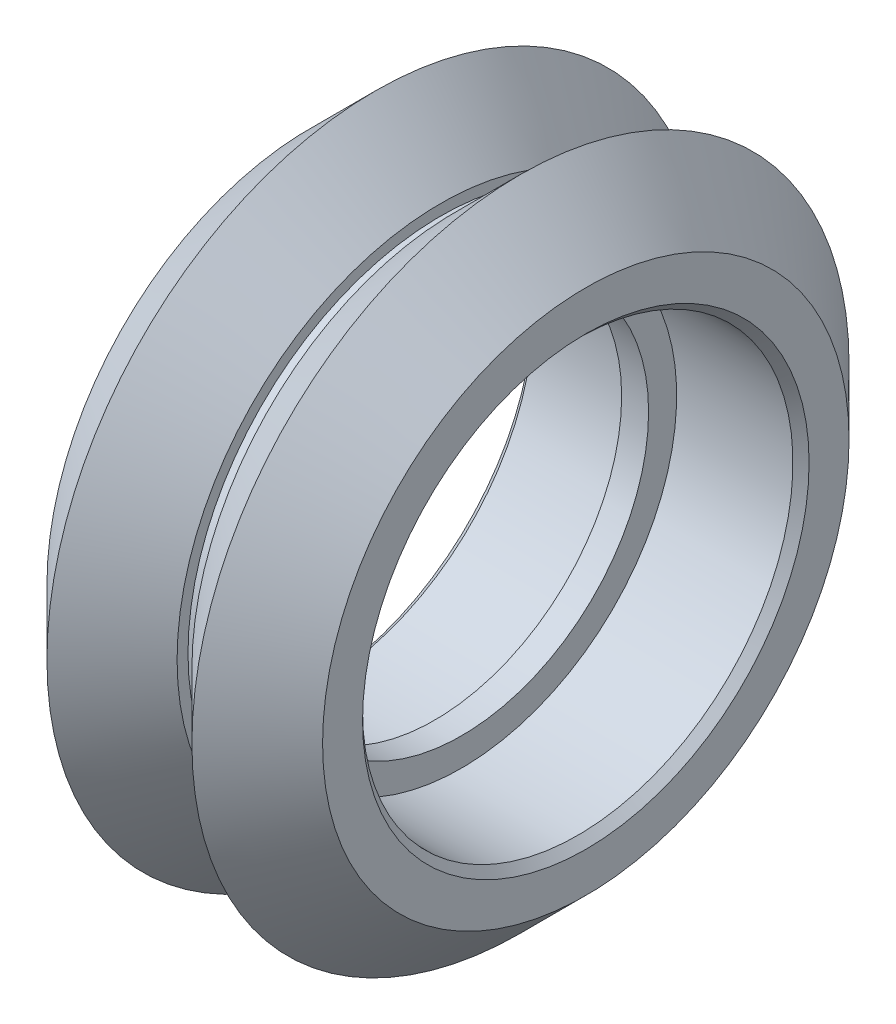
SolidWorks part; units mm, degrees
material "Delrin 2700 NC010, Low Viscosity Acetal Copolymer (SS)"
ref_plane "Front Plane" through (0, 0, 0) normal (0, 0, 1) x (1, 0, 0)
ref_plane "Top Plane" through (0, 0, 0) normal (0, 1, 0) x (1, 0, 0)
ref_plane "Right Plane" through (0, 0, 0) normal (1, 0, 0) x (0, 0, -1)
sketch "Sketch1" plane through (0, 0, 0) normal (0, 0, 1) x (1, 0, 0)
  line L0 (0.5, 6.945) -> (-0.5, 6.945)
  line L1 (-0.5, 6.945) -> (-0.5, 7.987)
  line L2 (-0.5, 7.987) -> (-5.115, 7.987)
  line L3 (-5.115, 7.987) -> (-5.115, 9.77)
  line L4 (-5.115, 9.77) -> (-2.69, 12.195)
  line L5 (-2.69, 12.195) -> (-0.275, 9.78)
  line L6 (-0.275, 9.78) -> (-0.275, 9.375)
  line L7 (-0.275, 9.375) -> (0.275, 9.375)
  line L8 (0.275, 9.375) -> (0.275, 9.78)
  line L9 (0.275, 9.78) -> (2.69, 12.195)
  line L10 (2.69, 12.195) -> (5.115, 9.77)
  line L11 (5.115, 9.77) -> (5.115, 7.987)
  line L12 (5.115, 7.987) -> (0.5, 7.987)
  line L13 (0.5, 7.987) -> (0.5, 6.945)
  line L14 (0, 0) -> (0, 6.7487) construction
  line L15 (0, 0) -> (6.3888, 0) construction
  dimension "D1" = 1
  dimension "D2" = 10.23
  dimension "D3" = 0.55
  dimension "D4" = 90
  dimension "D5" = 12.195
  dimension "D6" = 135
  dimension "D7" = 9.77
  dimension "D8" = 7.987
  dimension "D9" = 9.375
  dimension "D10" = 6.945
revolve "Revolve1" add sketch "Sketch1" angle 360 about L15
chamfer "Chamfer1" distance 0.3 angle 45 2 edges at (5.115, 0, 7.987) (-5.115, 0, 7.987)
